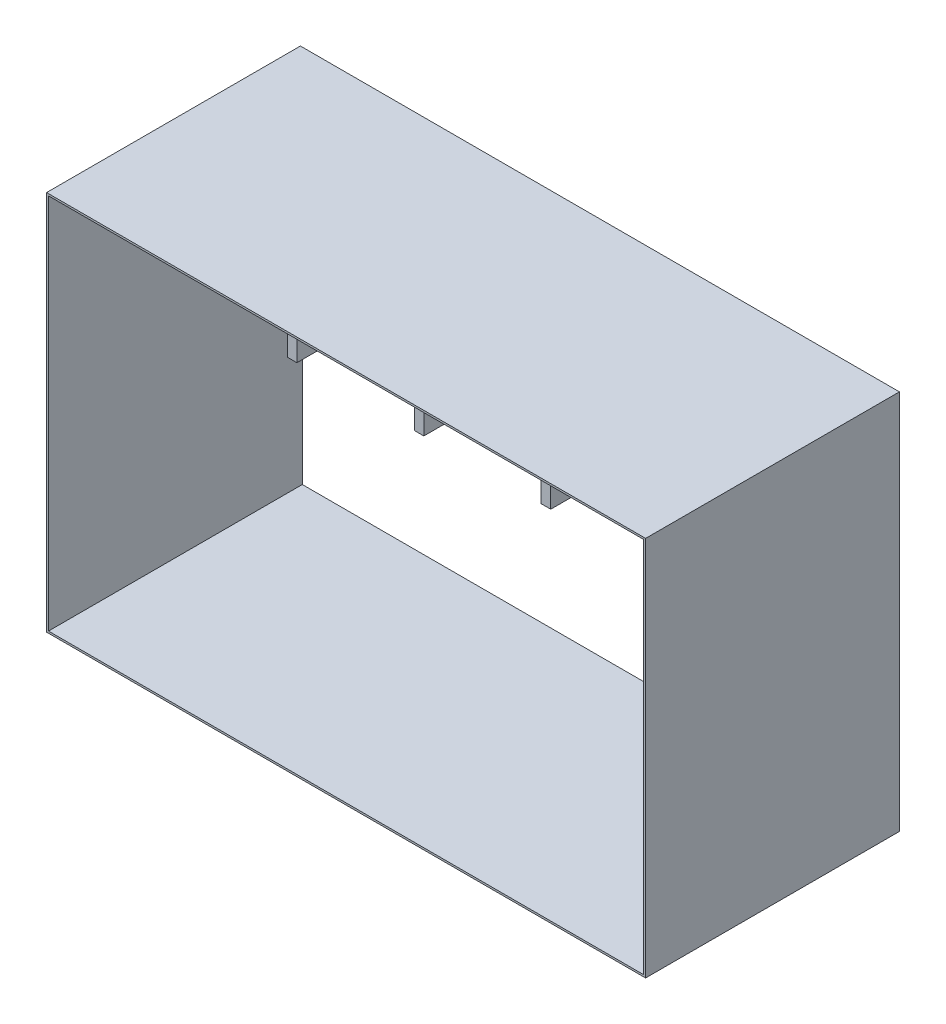
SolidWorks part; units mm, degrees
ref_plane "Alzado" through (0, 0, 0) normal (0, 0, 1) x (1, 0, 0)
ref_plane "Planta" through (0, 0, 0) normal (0, 1, 0) x (1, 0, 0)
ref_plane "Vista lateral" through (0, 0, 0) normal (1, 0, 0) x (0, 0, -1)
sketch "Croquis1" plane through (0, 0, 0) normal (0, 0, 1) x (1, 0, 0)
  line L1 (-472, -300) -> (472, -300)
  line L2 (-472, -300) -> (-472, 300)
  line L3 (-472, 300) -> (472, 300)
  line L4 (472, -300) -> (472, 300)
  line L5 (-472, -300) -> (472, 300) construction
  line L6 (-472, 300) -> (472, -300) construction
  point P0 (0, 0)
  dimension "D1" = 944
  dimension "D2" = 600
extrude "Saliente-Extruir1" add sketch "Croquis1" along normal blind 400
sketch "Croquis2" plane through (0, 0, 400) normal (0, 0, 1) x (1, 0, 0)
  line L0 (472, 300) -> (-472, 300) construction
  line L1 (469, -297) -> (-469, -297)
  line L2 (469, -297) -> (469, 297)
  line L3 (469, 297) -> (-469, 297)
  line L4 (-469, -297) -> (-469, 297)
  line L5 (469, -297) -> (-469, 297) construction
  line L6 (469, 297) -> (-469, -297) construction
  line L7 (-472, 300) -> (-472, -300) construction
  point P0 (0, 0)
  dimension "D1" = 3
  dimension "D2" = 3
extrude "Cortar-Extruir1" cut sketch "Croquis2" against normal blind 400
sketch "Croquis3" plane through (0, 0, 0) normal (0, 0, -1) x (-1, 0, 0)
  line L0 (472, 300) -> (472, -300) construction
  line L1 (-307.5, 50) -> (-292.5, 50)
  line L2 (-307.5, 50) -> (-307.5, 150)
  line L3 (-307.5, 150) -> (-292.5, 150)
  line L4 (-292.5, 50) -> (-292.5, 150)
  line L5 (-307.5, 50) -> (-292.5, 150) construction
  line L6 (-307.5, 150) -> (-292.5, 50) construction
  line L7 (-107.5, 50) -> (-92.5, 50)
  line L8 (-107.5, 50) -> (-107.5, 150)
  line L9 (-107.5, 150) -> (-92.5, 150)
  line L10 (-92.5, 50) -> (-92.5, 150)
  line L11 (-107.5, 50) -> (-92.5, 150) construction
  line L12 (-107.5, 150) -> (-92.5, 50) construction
  line L13 (92.5, 50) -> (107.5, 50)
  line L14 (92.5, 50) -> (92.5, 150)
  line L15 (92.5, 150) -> (107.5, 150)
  line L16 (107.5, 50) -> (107.5, 150)
  line L17 (92.5, 50) -> (107.5, 150) construction
  line L18 (92.5, 150) -> (107.5, 50) construction
  line L19 (292.5, 50) -> (307.5, 50)
  line L20 (292.5, 50) -> (292.5, 150)
  line L21 (292.5, 150) -> (307.5, 150)
  line L22 (307.5, 50) -> (307.5, 150)
  line L23 (292.5, 50) -> (307.5, 150) construction
  line L24 (292.5, 150) -> (307.5, 50) construction
  line L26 (-472, 300) -> (472, 300) construction
  point P0 (-300, 100)
  point P5 (-100, 100)
  point P10 (100, 100)
  point P15 (300, 100)
  point P20 (-100, 150)
  point P21 (100, 150)
  point P22 (300, 150)
  point P23 (-300, 150)
  point P24 (-181.5394, 180.0137)
  dimension "D1" = 15
  dimension "D2" = 15
  dimension "D3" = 100
  dimension "D4" = 100
  dimension "D5" = 100
  dimension "D6" = 15
  dimension "D7" = 100
  dimension "D8" = 15
  dimension "D9" = 200
  dimension "D10" = 200
  dimension "D11" = 200
  dimension "D12" = 164.5
  dimension "D13" = 150
  dimension "D14" = 150
  dimension "D15" = 150
  dimension "D16" = 150
extrude "Saliente-Extruir2" add sketch "Croquis3" against normal blind 185 separate body
sketch "Croquis5" plane through (-307.5, 0, 0) normal (-1, 0, 0) x (0, 0, 1)
  line L0 (185, 150) -> (0, 150) construction
  line L1 (185, 50) -> (185, 150) construction
  line L2 (185, 50) -> (0, 50) construction
  circle A0 centre (155, 122) radius 8
  circle A1 centre (155, 78) radius 8
  circle A2 centre (110, 122) radius 8
  circle A3 centre (110, 78) radius 8
  dimension "D1" = 16
  dimension "D3" = 30
  dimension "D4" = 16
  dimension "D6" = 30
  dimension "D7" = 16
  dimension "D8" = 45
  dimension "D9" = 16
  dimension "D10" = 45
  dimension "D2" = 28
  dimension "D5" = 28
  dimension "D11" = 28
extrude "Cortar-Extruir2" cut sketch "Croquis5" against normal up to surface (615 mm away) up to face at (307.5, 100, 92.5)
